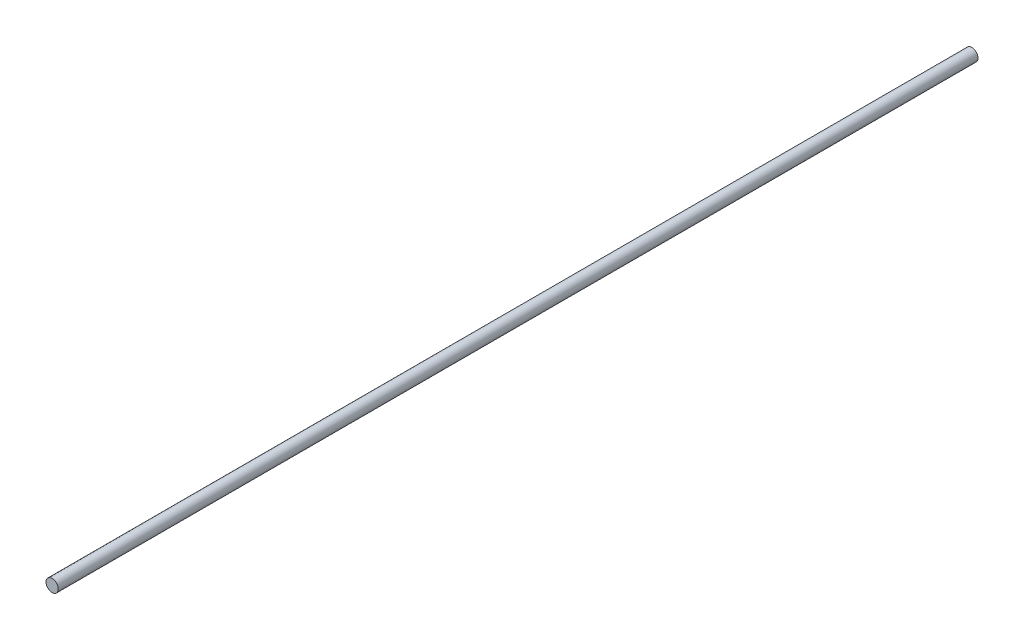
SolidWorks part; units mm, degrees
ref_plane "前视基准面" through (0, 0, 0) normal (0, 0, 1) x (1, 0, 0)
ref_plane "上视基准面" through (0, 0, 0) normal (0, 1, 0) x (1, 0, 0)
ref_plane "右视基准面" through (0, 0, 0) normal (1, 0, 0) x (0, 0, -1)
sketch "草图1" plane through (0, 0, 0) normal (0, 0, 1) x (1, 0, 0)
  circle A0 centre (0, 0) radius 4
extrude "凸台-拉伸1" add sketch "草图1" along normal blind 600
